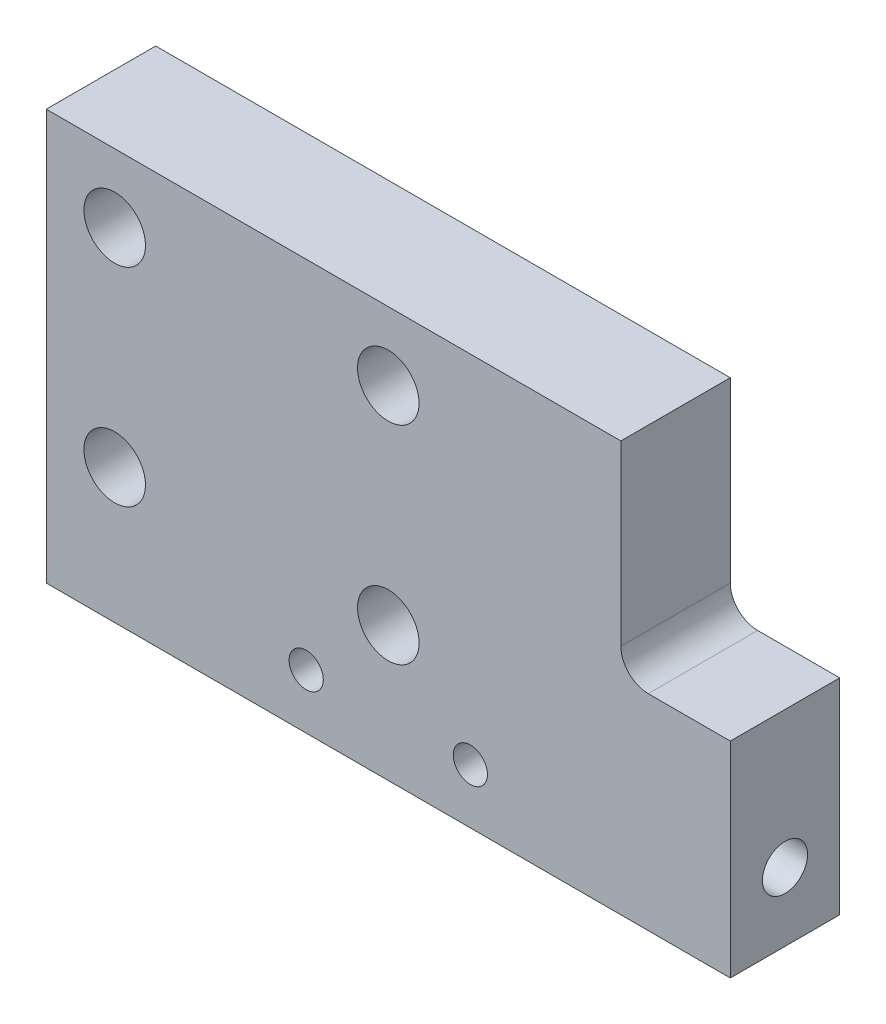
SolidWorks part; units mm, degrees
ref_plane "Front Plane" through (0, 0, 0) normal (0, 0, 1) x (1, 0, 0)
ref_plane "Top Plane" through (0, 0, 0) normal (0, 1, 0) x (1, 0, 0)
ref_plane "Right Plane" through (0, 0, 0) normal (1, 0, 0) x (0, 0, -1)
sketch "Sketch2" plane through (0, 0, 0) normal (0, 0, 1) x (1, 0, 0)
  line L1 (-21.6292, 13.0337) -> (20.3708, 13.0337)
  line L2 (-21.6292, 13.0337) -> (-21.6292, -16.9663)
  line L3 (-21.6292, -16.9663) -> (28.3708, -16.9663)
  line L4 (28.3708, -1.9663) -> (28.3708, -16.9663)
  line L6 (20.3708, 13.0337) -> (20.3708, -1.9663)
  line L7 (20.3708, -1.9663) -> (28.3708, -1.9663)
  circle A0 centre (-16.6292, 8.0337) radius 2.25
  circle A1 centre (3.3708, 8.0337) radius 2.25
  circle A2 centre (-16.6292, -7.1348) radius 2.25
  circle A3 centre (3.3708, -7.1348) radius 2.25
  point P14 (0, 0)
  point P15 (0, 0)
  point P16 (0, 0)
  point P17 (0, 0)
  dimension "D5" = 4.5
  dimension "D6" = 25
  dimension "D7" = 45
  dimension "D1" = 50
  dimension "D2" = 30
  dimension "D3" = 15
  dimension "D4" = 8
  dimension "D8" = 25
extrude "Boss-Extrude1" add sketch "Sketch2" along normal blind 8
hole_wizard "M3 Tapped Hole1" positions "Sketch3" profile "Sketch4" tap size "M3" standard "ISO"
sketch "Sketch3" plane through (0, 0, 8) normal (0, 0, 1) x (1, 0, 0)
  line L0 (28.3708, -16.9663) -> (28.3708, -1.9663) construction
  line L1 (-21.6292, -16.9663) -> (28.3708, -16.9663) construction
  point P0 (-2.6292, -12.9663)
  point P2 (9.3708, -12.9663)
  dimension "D1" = 19
  dimension "D2" = 31
  dimension "D3" = 4
  dimension "D4" = 4
sketch "Sketch4" plane through (-2.6292, -12.9663, 8) normal (1, 0, 0) x (0, -1, 0)
  line L0 (0, 0) -> (0, 8.2511)
  line L1 (0, 8.2511) -> (1.25, 7.5)
  line L2 (1.25, 7.5) -> (1.25, 0)
  line L5 (1.25, 0) -> (0, 0)
  line L10 (0, 8.2511) -> (-1.25, 7.5) construction
  line L11 (0, -6.35) -> (0, 107.95) construction
  dimension "Tap Drill Dia." = 2.5
  dimension "Tap Drill Depth" = 7.5
  dimension "Drill Angle" = 118
cosmetic thread "Hole Thread1" parameters "D1"=6, "D2"=3
cosmetic thread "Hole Thread2" parameters "D1"=6, "D2"=3
hole_wizard "M4 Tapped Hole1" positions "Sketch5" profile "Sketch6" tap size "M4" standard "ISO"
sketch "Sketch5" plane through (28.3708, 0, 0) normal (1, 0, 0) x (0, 0, -1)
  line L0 (-8, -16.9663) -> (0, -16.9663) construction
  line L1 (0, -16.9663) -> (0, -1.9663) construction
  point P0 (-4, -11.9663)
  dimension "D1" = 5
  dimension "D2" = 4
sketch "Sketch6" plane through (28.3708, -11.9663, 4) normal (0, 1, 0) x (0, 0, -1)
  line L0 (0, 0) -> (0, 8.9914)
  line L1 (0, 8.9914) -> (1.65, 8)
  line L2 (1.65, 8) -> (1.65, 0)
  line L5 (1.65, 0) -> (0, 0)
  line L10 (0, 8.9914) -> (-1.65, 8) construction
  line L11 (0, -6.35) -> (0, 107.95) construction
  dimension "Tap Drill Dia." = 3.3
  dimension "Tap Drill Depth" = 8
  dimension "Drill Angle" = 118
cosmetic thread "Hole Thread3" parameters "D1"=8, "D2"=4
hole_wizard "M4 Tapped Hole2" positions "Sketch7" profile "Sketch8" tap size "M4" standard "ISO"
sketch "Sketch7" plane through (-21.6292, 0, 0) normal (-1, 0, 0) x (0, 0, 1)
  line L0 (8, 13.0337) -> (8, -16.9663) construction
  line L1 (8, -16.9663) -> (0, -16.9663) construction
  point P0 (4, -11.9663)
  dimension "D1" = 4
  dimension "D2" = 5
sketch "Sketch8" plane through (-21.6292, -11.9663, 4) normal (0, 1, 0) x (0, 0, 1)
  line L0 (0, 0) -> (0, 8.9914)
  line L1 (0, 8.9914) -> (1.65, 8)
  line L2 (1.65, 8) -> (1.65, 0)
  line L5 (1.65, 0) -> (0, 0)
  line L10 (0, 8.9914) -> (-1.65, 8) construction
  line L11 (0, -6.35) -> (0, 107.95) construction
  dimension "Tap Drill Dia." = 3.3
  dimension "Tap Drill Depth" = 8
  dimension "Drill Angle" = 118
cosmetic thread "Hole Thread4" parameters "D1"=8, "D2"=4
fillet "Fillet1" radius 2 1 edges at (20.3708, -1.9663, 4)
